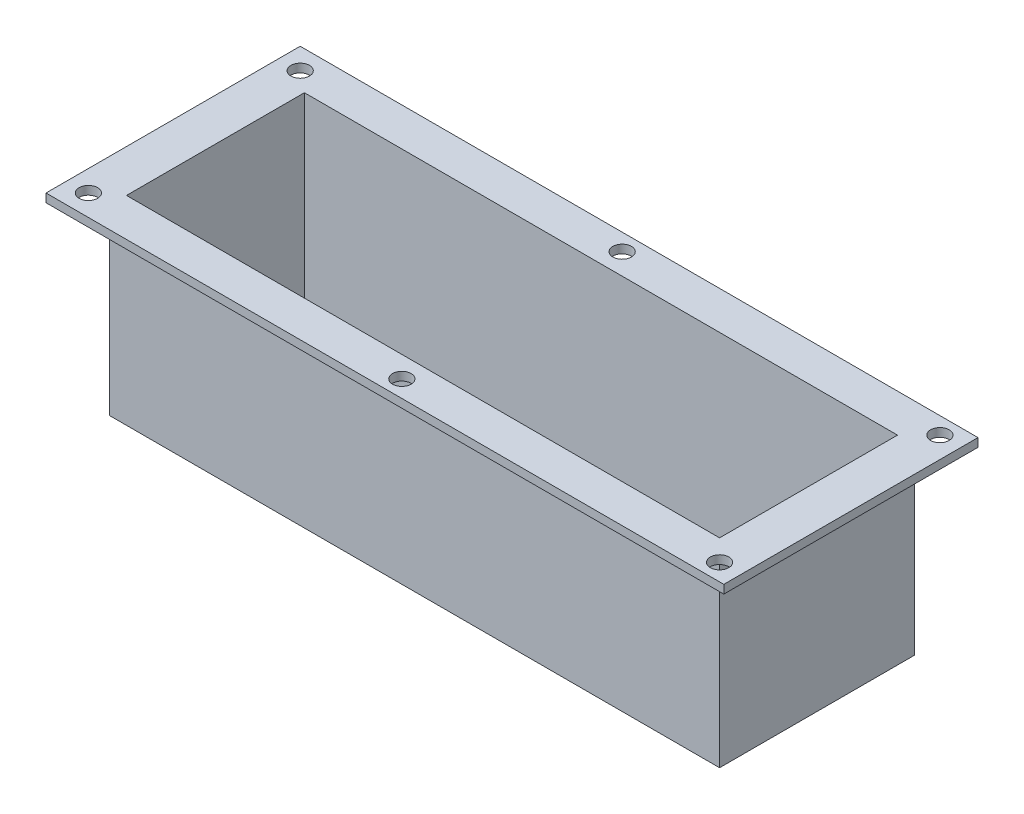
SolidWorks part; units mm, degrees
ref_plane "Front Plane" through (0, 0, 0) normal (0, 0, 1) x (1, 0, 0)
ref_plane "Top Plane" through (0, 0, 0) normal (0, 1, 0) x (1, 0, 0)
ref_plane "Right Plane" through (0, 0, 0) normal (1, 0, 0) x (0, 0, -1)
sketch "Sketch3" plane through (0, 0, 0) normal (0, 1, 0) x (1, 0, 0)
  line L1 (-91.44, 29.21) -> (91.44, 29.21)
  line L2 (-91.44, 29.21) -> (-91.44, -29.21)
  line L3 (-91.44, -29.21) -> (91.44, -29.21)
  line L4 (91.44, 29.21) -> (91.44, -29.21)
  line L5 (-91.44, 29.21) -> (91.44, -29.21) construction
  line L6 (-91.44, -29.21) -> (91.44, 29.21) construction
  point P0 (0, 0)
  dimension "D1" = 58.42
  dimension "D2" = 182.88
extrude "Boss-Extrude1" add sketch "Sketch3" against normal blind 57.15
sketch "Sketch4" plane through (0, 0, 0) normal (0, 1, 0) x (1, 0, 0)
  line L1 (-101.6, -38.1) -> (101.6, -38.1)
  line L2 (-101.6, -38.1) -> (-101.6, 38.1)
  line L3 (-101.6, 38.1) -> (101.6, 38.1)
  line L4 (101.6, -38.1) -> (101.6, 38.1)
  line L5 (-101.6, -38.1) -> (101.6, 38.1) construction
  line L6 (-101.6, 38.1) -> (101.6, -38.1) construction
  point P0 (0, 0)
  dimension "D1" = 76.2
  dimension "D2" = 203.2
extrude "Boss-Extrude2" add sketch "Sketch4" against normal blind 2.54
sketch "Sketch5" plane through (0, 0, 0) normal (0, 1, 0) x (1, 0, 0)
  line L1 (-88.9, -26.67) -> (88.9, -26.67)
  line L2 (-88.9, -26.67) -> (-88.9, 26.67)
  line L3 (-88.9, 26.67) -> (88.9, 26.67)
  line L4 (88.9, -26.67) -> (88.9, 26.67)
  line L5 (-88.9, -26.67) -> (88.9, 26.67) construction
  line L6 (-88.9, 26.67) -> (88.9, -26.67) construction
  point P0 (0, 0)
  dimension "D1" = 53.34
  dimension "D2" = 177.8
extrude "Cut-Extrude1" cut sketch "Sketch5" against normal blind 54.61
sketch "Sketch6" plane through (0, 0, 0) normal (0, 1, 0) x (1, 0, 0)
  line L0 (88.9, 26.67) -> (-88.9, 26.67) construction
  line L1 (-88.9, 26.67) -> (-88.9, -26.67) construction
  line L2 (88.9, -26.67) -> (88.9, 26.67) construction
  line L3 (-118.5656, 0) -> (108.8741, 0) construction
  circle A0 centre (-95.25, 31.75) radius 2.7813
  circle A1 centre (0, 33.02) radius 2.7813
  circle A2 centre (95.25, 33.02) radius 2.7813
  circle A3 centre (95.25, -33.02) radius 2.7813
  circle A4 centre (0, -33.02) radius 2.7813
  circle A5 centre (-95.25, -31.75) radius 2.7813
  dimension "D1" = 5.5626
  dimension "D4" = 5.5626
  dimension "D6" = 5.5626
  dimension "D2" = 5.08
  dimension "D3" = 6.35
  dimension "D5" = 6.35
  dimension "D7" = 6.35
  dimension "D8" = 6.35
extrude "Cut-Extrude2" cut sketch "Sketch6" against normal blind 53.34
sketch "Sketch7" plane through (0, -54.61, 0) normal (0, 1, 0) x (1, 0, 0)
  line L0 (-88.9, 25.4) -> (-88.9, -25.4) construction
  line L2 (-88.9, -25.4) -> (-38.1, -25.4) construction
  line L3 (-63.5, -25.4) -> (-63.5, 0) construction
  circle A1 centre (-63.5, 12.7) radius 3.175
  circle A2 centre (-50.8, 0) radius 3.175
  circle A3 centre (-63.5, -12.7) radius 3.175
  circle A4 centre (-76.2, 0) radius 3.175
  point P2 (-88.9, 0)
  dimension "D3" = 12.7
  dimension "D6" = 6.35
  dimension "D7" = 4
  dimension "D1" = 50.8
  dimension "D2" = 88.9
  dimension "D4" = 25.4
  dimension "D5" = 25.4
extrude "Cut-Extrude3" cut sketch "Sketch7" against normal through all
